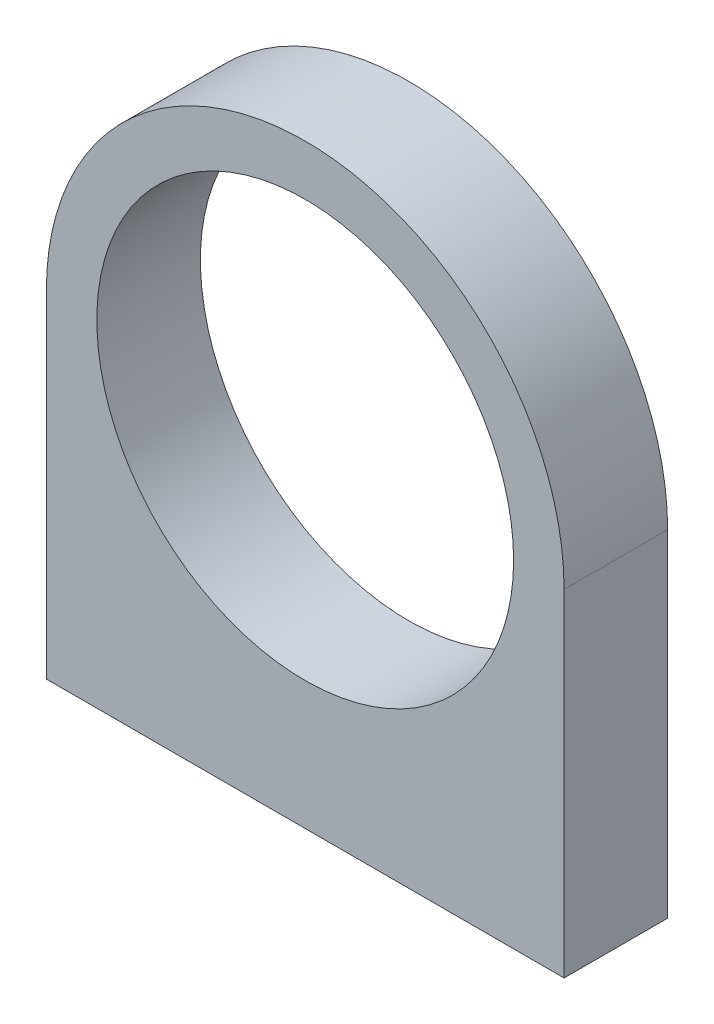
SolidWorks part; units mm, degrees
ref_plane "Plan de face" through (0, 0, 0) normal (0, 0, 1) x (1, 0, 0)
ref_plane "Plan de dessus" through (0, 0, 0) normal (0, 1, 0) x (1, 0, 0)
ref_plane "Plan de droite" through (0, 0, 0) normal (1, 0, 0) x (0, 0, -1)
sketch "Esquisse1" plane through (0, 0, 0) normal (0, 0, 1) x (1, 0, 0)
  line L1 (-20, 0) -> (20, 0) construction
  line L2 (-20, 0) -> (-20, -26)
  line L3 (-20, -26) -> (20, -26)
  line L4 (20, 0) -> (20, -26)
  circle A0 centre (0, 0) radius 20 construction
  arc A1 (-20, 0) -> (20, 0) centre (0, 0) cw
  circle A2 centre (0, 0) radius 16.1
  dimension "D1" = 40
  dimension "D3" = 32.2
  dimension "D2" = 26
extrude "Boss.-Extru.1" add sketch "Esquisse1" along normal blind 8
sketch "Esquisse2" plane through (0, -26, 0) normal (0, -1, 0) x (1, 0, 0)
  line L0 (-16, 4) -> (16, 4) construction
  line L1 (0, 0) -> (0, 8) construction
  line L2 (-20, 8) -> (20, 8) construction
  line L3 (-20, 8) -> (-20, 0) construction
  circle A0 centre (-16, 4) radius 1.25
  circle A1 centre (16, 4) radius 1.25
  point P8 (0, 4)
  point P9 (0, 4)
  dimension "D1" = 2.5
  dimension "D2" = 4
extrude "Enlèv. mat.-Extru.1" cut sketch "Esquisse2" against normal blind 15
